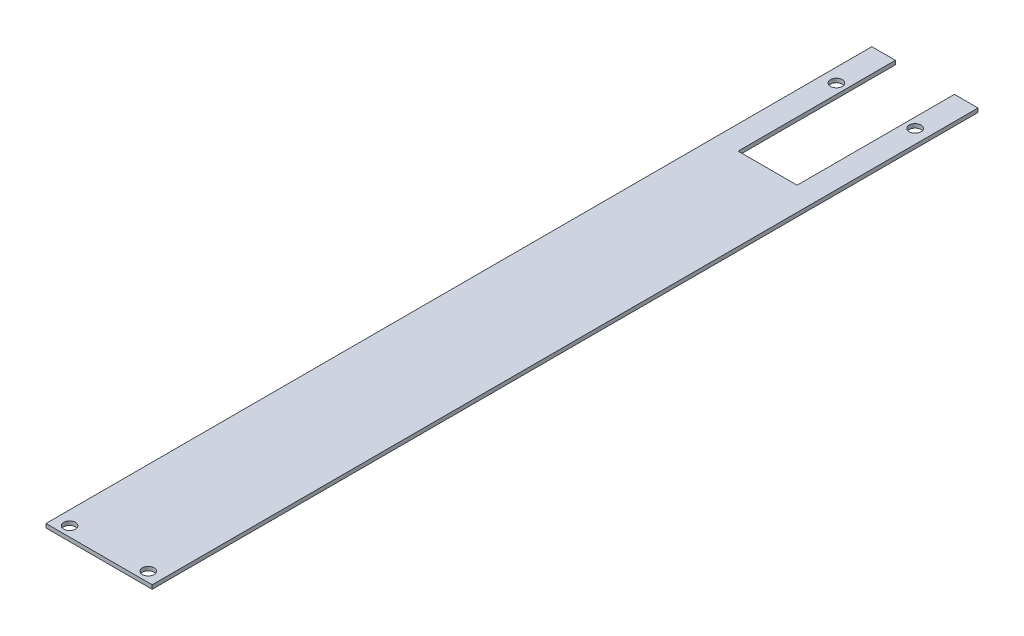
SolidWorks part; units mm, degrees
ref_plane "Front Plane" through (0, 0, 0) normal (0, 0, 1) x (1, 0, 0)
ref_plane "Top Plane" through (0, 0, 0) normal (0, 1, 0) x (1, 0, 0)
ref_plane "Right Plane" through (0, 0, 0) normal (1, 0, 0) x (0, 0, -1)
sketch "Sketch1" plane through (0, 100, 0) normal (0, 1, 0) x (-1, 0, 0)
  line L1 (28.0517, 394.6922) -> (-25.9483, 394.6922)
  line L2 (28.0517, 394.6922) -> (28.0517, -25.3078)
  line L3 (28.0517, -25.3078) -> (-25.9483, -25.3078)
  line L4 (-25.9483, 394.6922) -> (-25.9483, -25.3078)
extrude "Boss-Extrude1" add sketch "Sketch1" along normal blind 2
sketch "Sketch2" plane through (0, 102, 0) normal (0, 1, 0) x (-1, 0, 0)
  line L0 (-25.9483, -25.3078) -> (28.0517, -25.3078) construction
  line L1 (16.0517, -25.3078) -> (-13.9483, -25.3078)
  line L2 (16.0517, -25.3078) -> (16.0517, 54.6922)
  line L3 (16.0517, 54.6922) -> (-13.9483, 54.6922)
  line L4 (-13.9483, -25.3078) -> (-13.9483, 54.6922)
  line L5 (28.0517, -25.3078) -> (28.0517, 394.6922) construction
  line L6 (-25.9483, 394.6922) -> (-25.9483, -25.3078) construction
  dimension "D1" = 12
  dimension "D2" = 12
  dimension "D3" = 80
extrude "Cut-Extrude1" cut sketch "Sketch2" against normal up to next
sketch "Sketch3" plane through (0, 102, 0) normal (0, 1, 0) x (-1, 0, 0)
  circle A0 centre (-18.9483, -0.3078) radius 3
  circle A1 centre (21.0517, -0.3078) radius 3
  circle A2 centre (21.0517, 389.6922) radius 3
  circle A3 centre (-18.9483, 389.6922) radius 3
  dimension "D1" = 6
  dimension "D2" = 6
  dimension "D3" = 6
  dimension "D4" = 6
extrude "Cut-Extrude2" cut sketch "Sketch3" against normal up to next
